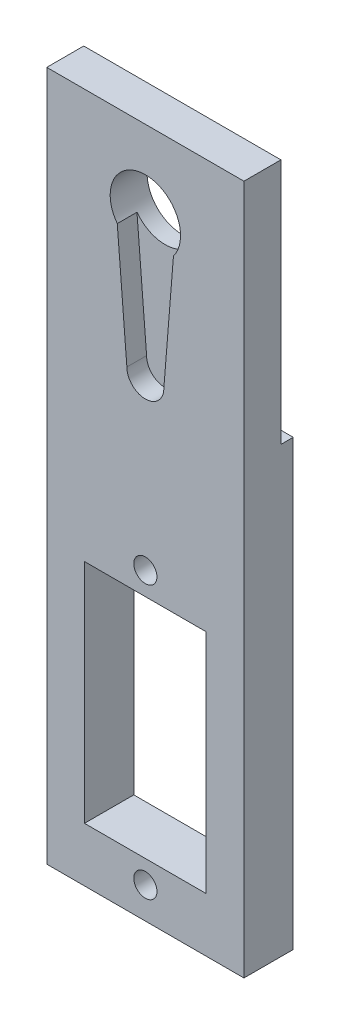
SolidWorks part; units mm, degrees
ref_plane "Front Plane" through (0, 0, 0) normal (0, 0, 1) x (1, 0, 0)
ref_plane "Top Plane" through (0, 0, 0) normal (0, 1, 0) x (1, 0, 0)
ref_plane "Right Plane" through (0, 0, 0) normal (1, 0, 0) x (0, 0, -1)
sketch "Sketch3" plane through (0, 0, 0) normal (0, 0, 1) x (1, 0, 0)
  line L1 (-10, 35) -> (10, 35)
  line L2 (-10, 35) -> (-10, -35)
  line L3 (-10, -35) -> (10, -35)
  line L4 (10, 35) -> (10, -35)
  line L5 (-10, 35) -> (10, -35) construction
  line L6 (-10, -35) -> (10, 35) construction
  point P0 (0, 0)
  dimension "D1" = 20
  dimension "D2" = 70
extrude "Boss-Extrude3" add sketch "Sketch3" along normal blind 5
sketch "Sketch4" plane through (0, 0, 5) normal (0, 0, 1) x (1, 0, 0)
  line L0 (-1.875, 12.7392) -> (1.875, 12.7392)
  line L1 (-2.85, 24.85) -> (2.85, 24.85)
  line L2 (-2.85, 24.85) -> (-1.875, 12.7392)
  line L3 (2.85, 24.85) -> (1.875, 12.7392)
  line L4 (10, -35) -> (10, 35) construction
  line L7 (10, 35) -> (-10, 35) construction
  circle A0 centre (0, 27) radius 3.57
  arc A1 (-1.875, 12.7392) -> (1.875, 12.7392) centre (0, 12.7392) ccw
  dimension "D1" = 7.14
  dimension "D2" = 3.75
  dimension "D3" = 5.7
  dimension "D4" = 12.15
  dimension "D5" = 12.15
  dimension "D6" = 10
  dimension "D7" = 8
extrude "Cut-Extrude2" cut sketch "Sketch4" against normal blind 2 contours L0 A1 | A0 L2 L0 L3
sketch "Sketch6" plane through (0, 0, 3) normal (0, 0, 1) x (1, 0, 0)
  line L0 (10, 35) -> (-10, 35) construction
  line L1 (-10, 35) -> (-10, -35) construction
  circle A0 centre (0, 27) radius 3.57
  dimension "D1" = 7.14
  dimension "D2" = 8
  dimension "D3" = 10
extrude "Cut-Extrude3" cut sketch "Sketch6" against normal blind 3
sketch "Sketch7" plane through (0, 0, 5) normal (0, 0, 1) x (1, 0, 0)
  line L0 (10, -35) -> (10, 35) construction
  line L1 (-6.175, -6.5) -> (6.175, -6.5)
  line L2 (-6.175, -6.5) -> (-6.175, -29.5)
  line L3 (-6.175, -29.5) -> (6.175, -29.5)
  line L4 (6.175, -6.5) -> (6.175, -29.5)
  line L5 (-6.175, -6.5) -> (6.175, -29.5) construction
  line L6 (-6.175, -29.5) -> (6.175, -6.5) construction
  line L7 (-10, -35) -> (10, -35) construction
  line L8 (0, -18) -> (16.5777, -18) construction
  circle A0 centre (0, -4.18) radius 1.175
  circle A1 centre (0, -31.82) radius 1.175
  point P0 (0, -18)
  dimension "D6" = 2.35
  dimension "D1" = 12.35
  dimension "D2" = 23
  dimension "D3" = 10
  dimension "D4" = 17
  dimension "D5" = 10
  dimension "D7" = 2.32
extrude "Cut-Extrude4" cut sketch "Sketch7" against normal blind 5
sketch "Sketch8" plane through (10, 0, 0) normal (1, 0, 0) x (0, 0, -1)
  line L6 (0, 35) -> (-1.25, 35)
  line L7 (0, 35) -> (0, 10)
  line L8 (0, 10) -> (-1.25, 10)
  line L9 (-1.25, 35) -> (-1.25, 10)
  dimension "D1" = 25
  dimension "D2" = 1.25
extrude "Cut-Extrude5" cut sketch "Sketch8" against normal blind 30
